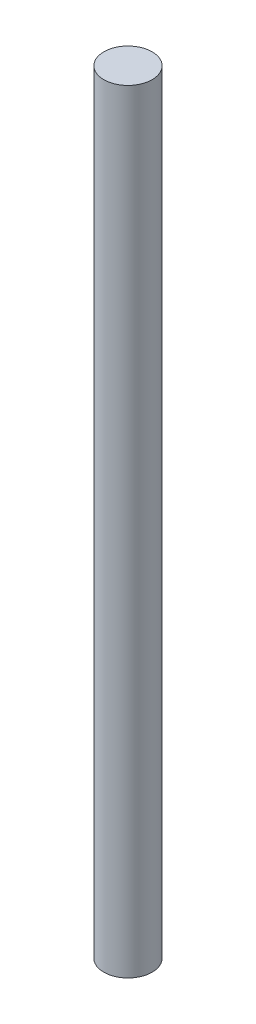
SolidWorks part; units mm, degrees
material "6061 Alloy"
ref_plane "Front Plane" through (0, 0, 0) normal (0, 0, 1) x (1, 0, 0)
ref_plane "Top Plane" through (0, 0, 0) normal (0, 1, 0) x (1, 0, 0)
ref_plane "Right Plane" through (0, 0, 0) normal (1, 0, 0) x (0, 0, -1)
sketch "Sketch1" plane through (0, 0, 0) normal (0, 1, 0) x (1, 0, 0)
  circle A0 centre (0, 0) radius 7.9375
  dimension "D1" = 15.875
extrude "Boss-Extrude1" add sketch "Sketch1" along normal blind 254
